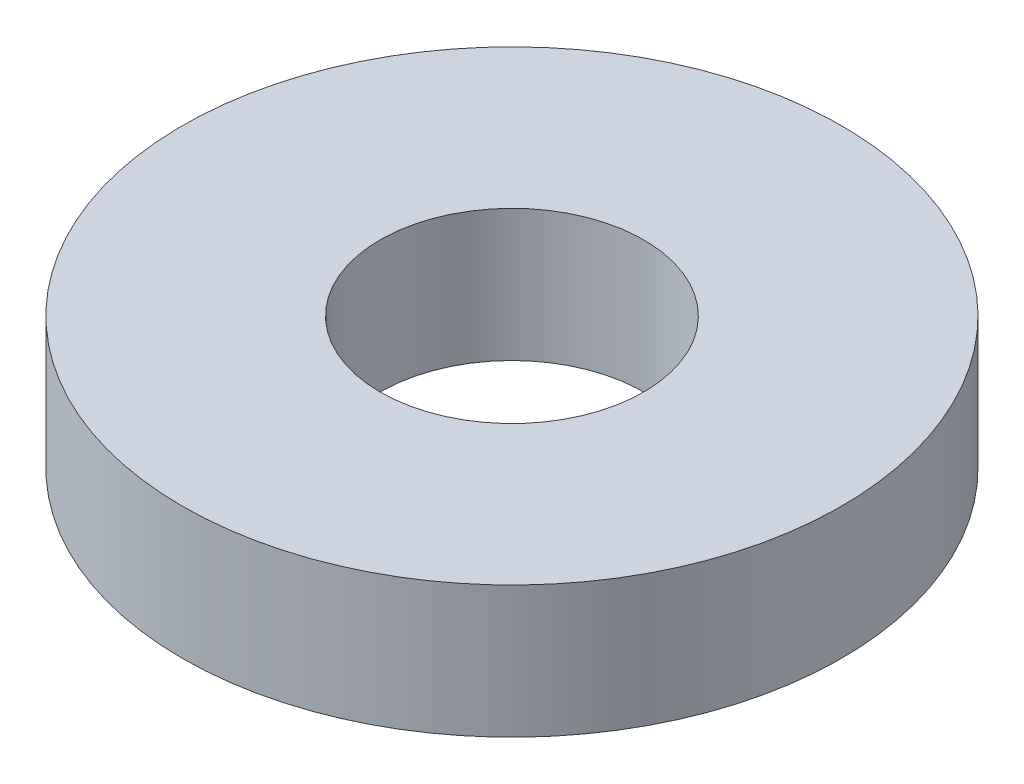
SolidWorks part; units mm, degrees
ref_plane "Front Plane" through (0, 0, 0) normal (0, 0, 1) x (1, 0, 0)
ref_plane "Top Plane" through (0, 0, 0) normal (0, 1, 0) x (1, 0, 0)
ref_plane "Right Plane" through (0, 0, 0) normal (1, 0, 0) x (0, 0, -1)
sketch "Sketch1" plane through (0, 0, 0) normal (0, 1, 0) x (1, 0, 0)
  circle A0 centre (0, 0) radius 5
  circle A1 centre (0, 0) radius 12.5
  dimension "D1" = 10
  dimension "D2" = 25
extrude "Boss-Extrude1" add sketch "Sketch1" along normal blind 5
